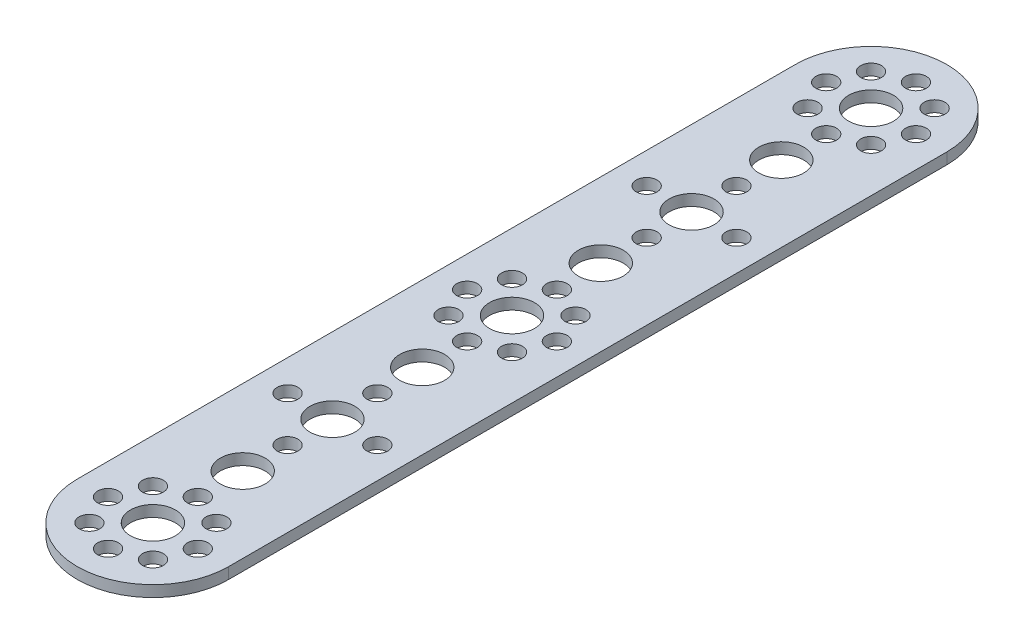
SolidWorks part; units mm, degrees
material "5052-H32"
ref_plane "Front Plane" through (0, 0, 0) normal (0, 0, 1) x (1, 0, 0)
ref_plane "Top Plane" through (0, 0, 0) normal (0, 1, 0) x (1, 0, 0)
ref_plane "Right Plane" through (0, 0, 0) normal (1, 0, 0) x (0, 0, -1)
sketch "Sketch1" plane through (0, 0, 0) normal (0, 1, 0) x (1, 0, 0)
  line L2 (-13.5, 64) -> (-13.5, -64)
  line L4 (13.5, 64) -> (13.5, -64)
  line L5 (-13.5, 80) -> (13.5, -80) construction
  line L6 (-13.5, -80) -> (13.5, 80) construction
  arc A0 (13.5, 64) -> (-13.5, 64) centre (0, 64) ccw
  arc A1 (-13.5, -64) -> (13.5, -64) centre (0, -64) ccw
  point P0 (0, 0)
  dimension "D1" = 160
  dimension "D2" = 27
  dimension "D3" = 64
  dimension "D4" = 64
extrude "Extrude1" add sketch "Sketch1" along normal blind 2
sketch "Sketch2" plane through (0, 2, 0) normal (0, 1, 0) x (1, 0, 0)
  line L0 (0, -89.629) -> (0, 93.2214) construction
  circle B0 centre (0, -48) radius 4
  circle B1 centre (0, -16) radius 4
  circle B2 centre (-0.1754, 16) radius 4
  circle B3 centre (0, 48) radius 4
  circle B4 centre (0, -32) radius 4
  circle B5 centre (0, -24) radius 1.85
  circle B6 centre (0, -40) radius 1.85
  circle B7 centre (8, -32) radius 1.85
  circle B8 centre (-8, -32) radius 1.85
  circle B9 centre (0, -56) radius 1.85
  circle B10 centre (8, -64) radius 1.85
  circle B11 centre (0, -64) radius 4
  circle B12 centre (-8, -64) radius 1.85
  circle B13 centre (-5.66, -69.66) radius 1.85
  circle B14 centre (5.66, -69.66) radius 1.85
  circle B15 centre (0, -72) radius 1.85
  circle B16 centre (-5.66, -58.34) radius 1.85
  circle B17 centre (5.66, -58.34) radius 1.85
  circle B18 centre (0, 32) radius 4
  circle B19 centre (0, 40) radius 1.85
  circle B20 centre (0, 24) radius 1.85
  circle B21 centre (8, 32) radius 1.85
  circle B22 centre (-8, 32) radius 1.85
  circle B23 centre (0, 8) radius 1.85
  circle B24 centre (8, 0) radius 1.85
  circle B25 centre (0, 0) radius 4
  circle B26 centre (-8, 0) radius 1.85
  circle B27 centre (-5.66, -5.66) radius 1.85
  circle B28 centre (5.66, -5.66) radius 1.85
  circle B29 centre (0, -8) radius 1.85
  circle B30 centre (-5.66, 5.66) radius 1.85
  circle B31 centre (5.66, 5.66) radius 1.85
  circle B32 centre (0, 56) radius 1.85
  circle B33 centre (-8, 64) radius 1.85
  circle B34 centre (0, 64) radius 4
  circle B35 centre (8, 64) radius 1.85
  circle B36 centre (5.66, 69.66) radius 1.85
  circle B37 centre (-5.66, 69.66) radius 1.85
  circle B38 centre (0, 72) radius 1.85
  circle B39 centre (5.66, 58.34) radius 1.85
  circle B40 centre (-5.66, 58.34) radius 1.85
sketch_block_instance "TETRIX 160 Pattern-1"
sketch_block "TETRIX 160 Pattern" parameters "D1"=16, "D2"=16, "D3"=16, "D4"=16, "D5"=16, "D6"=16, "D7"=16, "D8"=16
extrude "Extrude2" cut sketch "Sketch2" against normal blind 2
